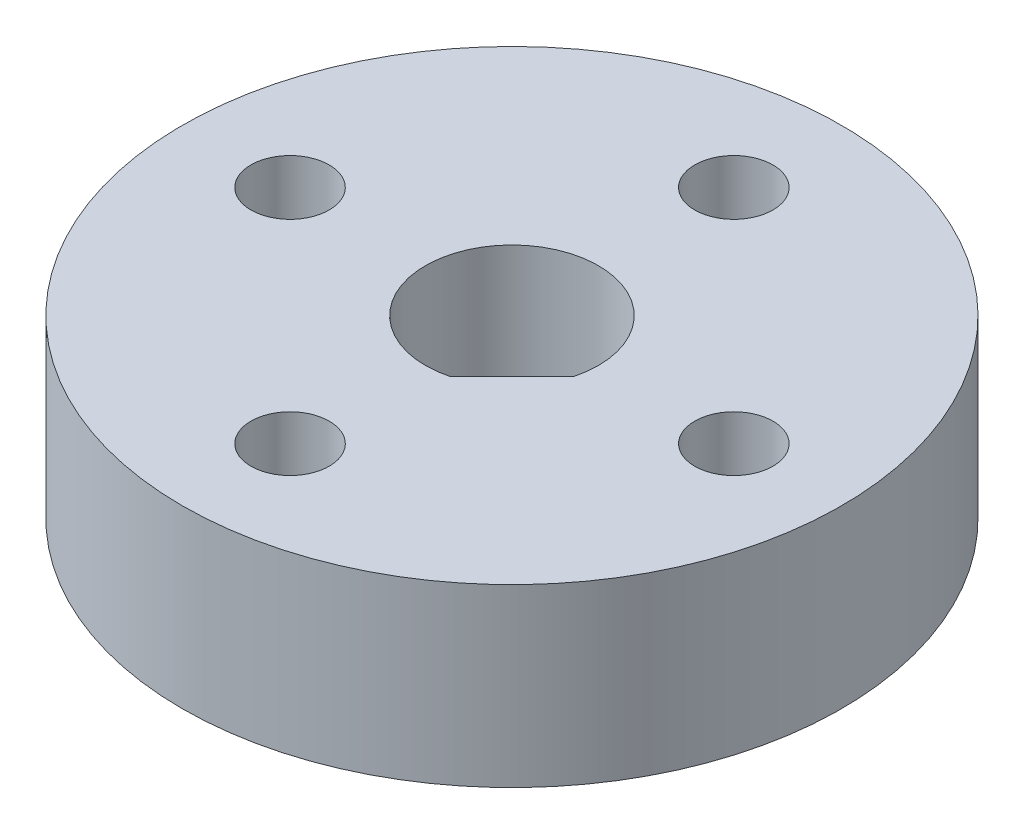
SolidWorks part; units mm, degrees
ref_plane "Front Plane" through (0, 0, 0) normal (0, 0, 1) x (1, 0, 0)
ref_plane "Top Plane" through (0, 0, 0) normal (0, 1, 0) x (1, 0, 0)
ref_plane "Right Plane" through (0, 0, 0) normal (1, 0, 0) x (0, 0, -1)
sketch "Sketch1" plane through (0, 0, 0) normal (0, 1, 0) x (1, 0, 0)
  line L0 (0, 0) -> (6.7352, -6.7352) construction
  line L1 (0.6247, -2.4207) -> (2.4207, -0.6247)
  line L2 (0, 0) -> (0, -9.525) construction
  circle A0 centre (0, 0) radius 9.525
  arc A1 (2.4207, -0.6247) -> (0.6247, -2.4207) centre (0, 0) ccw
  circle A2 centre (0, 0) radius 6.35 construction
  point P8 (1.5227, -1.5227)
  dimension "D1" = 19.05
  dimension "D2" = 5
  dimension "D3" = 12.7
  dimension "D4" = 45
  dimension "D5" = 2.54
extrude "Boss-Extrude1" add sketch "Sketch1" along normal blind 5.08
sketch "Sketch2" plane through (0, 0, 0) normal (0, 1, 0) x (1, 0, 0)
  line L0 (0, 0) -> (0, 6.35) construction
  circle A0 centre (0, 0) radius 6.35 construction
  circle A1 centre (0, 0) radius 6.35 construction
  point P5 (0, 6.35)
hole_wizard "#43 (0.089) Diameter Hole1" positions "Sketch3" profile "Sketch4" hole size "#43" standard "ANSI Inch" end condition through all
sketch "Sketch3" plane through (0, 5.08, 0) normal (0, 1, 0) x (1, 0, 0)
  point P0 (0, 6.4131)
sketch "Sketch4" plane through (0, 5.08, -6.4131) normal (1, 0, 0) x (0, 0, 1)
  line L0 (0, 0) -> (0, 5.08)
  line L1 (0, 5.08) -> (1.1303, 5.08)
  line L2 (1.1303, 5.08) -> (1.1303, 0)
  line L5 (1.1303, 0) -> (0, 0)
  line L11 (0, -6.35) -> (0, 107.95) construction
  dimension "Thru Hole Dia." = 2.2606
  dimension "Thru Hole Depth" = 5.08
pattern_circular "CirPattern1" count 4 over 360 about axis through (0, 0, 0) along (0, 1, 0) of "#43 (0.089) Diameter Hole1"
